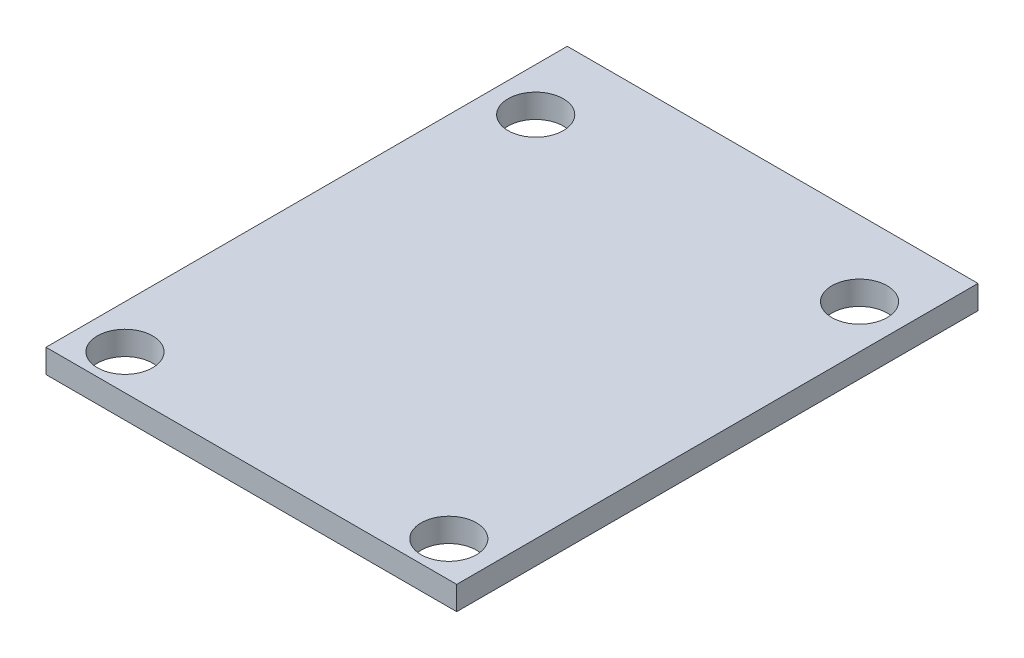
SolidWorks part; units mm, degrees
ref_plane "Front Plane" through (0, 0, 0) normal (0, 0, 1) x (1, 0, 0)
ref_plane "Top Plane" through (0, 0, 0) normal (0, 1, 0) x (1, 0, 0)
ref_plane "Right Plane" through (0, 0, 0) normal (1, 0, 0) x (0, 0, -1)
sketch "Sketch1" plane through (0, 0, 0) normal (0, 1, 0) x (1, 0, 0)
  line L1 (-13, 16.5) -> (13, 16.5)
  line L2 (-13, 16.5) -> (-13, -16.5)
  line L3 (-13, -16.5) -> (13, -16.5)
  line L4 (13, 16.5) -> (13, -16.5)
  line L5 (-13, 16.5) -> (13, -16.5) construction
  line L6 (-13, -16.5) -> (13, 16.5) construction
  circle A0 centre (-10.25, 11.75) radius 1.75
  circle A1 centre (10.25, 11.75) radius 1.75
  circle A2 centre (-10.25, -14.25) radius 1.75
  circle A3 centre (10.25, -14.25) radius 1.75
  point P0 (0, 0)
  point P14 (0, 0)
  point P15 (0, 0)
  point P16 (0, 0)
  point P17 (0, 0)
  point P18 (11.114, -12.706)
  point P19 (-9.1363, 13.3016)
  dimension "D3" = 3.5
  dimension "D1" = 26
  dimension "D2" = 33
  dimension "D4" = 2.75
  dimension "D5" = 2.75
  dimension "D6" = 4.75
  dimension "D7" = 2.25
extrude "Boss-Extrude1" add sketch "Sketch1" along normal blind 1.5 contours L4 L1 L2 L3 A3 A2 A1 A0
